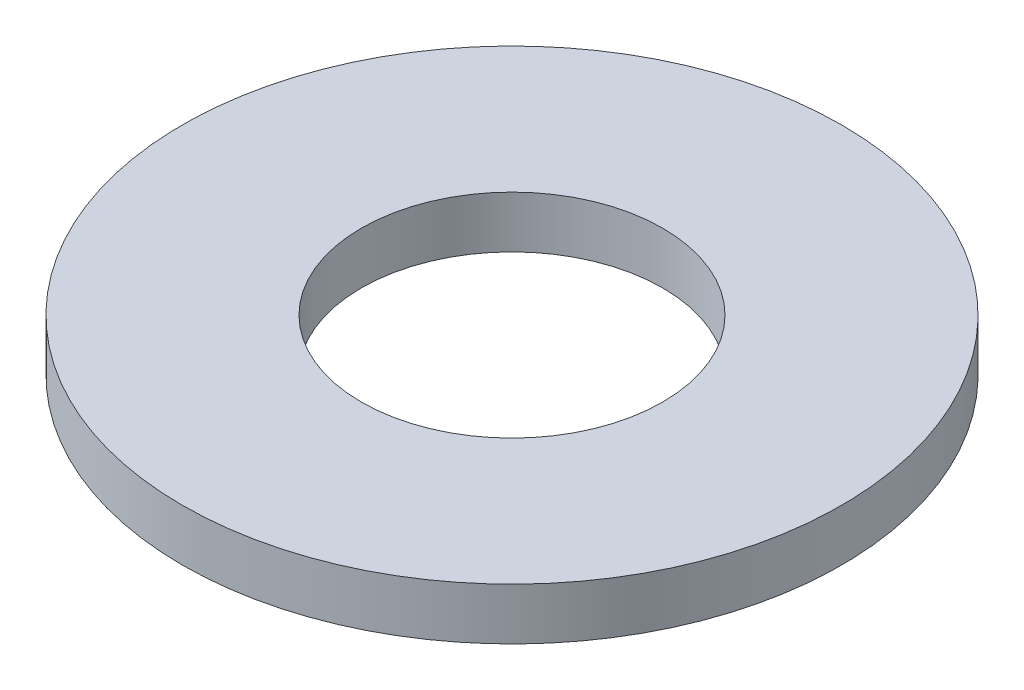
SolidWorks part; units mm, degrees
ref_plane "Front Plane" through (0, 0, 0) normal (0, 0, 1) x (1, 0, 0)
ref_plane "Top Plane" through (0, 0, 0) normal (0, 1, 0) x (1, 0, 0)
ref_plane "Right Plane" through (0, 0, 0) normal (1, 0, 0) x (0, 0, -1)
sketch "Sketch1" plane through (0, 0, 0) normal (0, 1, 0) x (1, 0, 0)
  circle A0 centre (0, 0) radius 1.6
  circle A1 centre (0, 0) radius 3.5
  dimension "D1" = 7
  dimension "D2" = 3.2
extrude "Boss-Extrude1" add sketch "Sketch1" along normal blind 0.55
